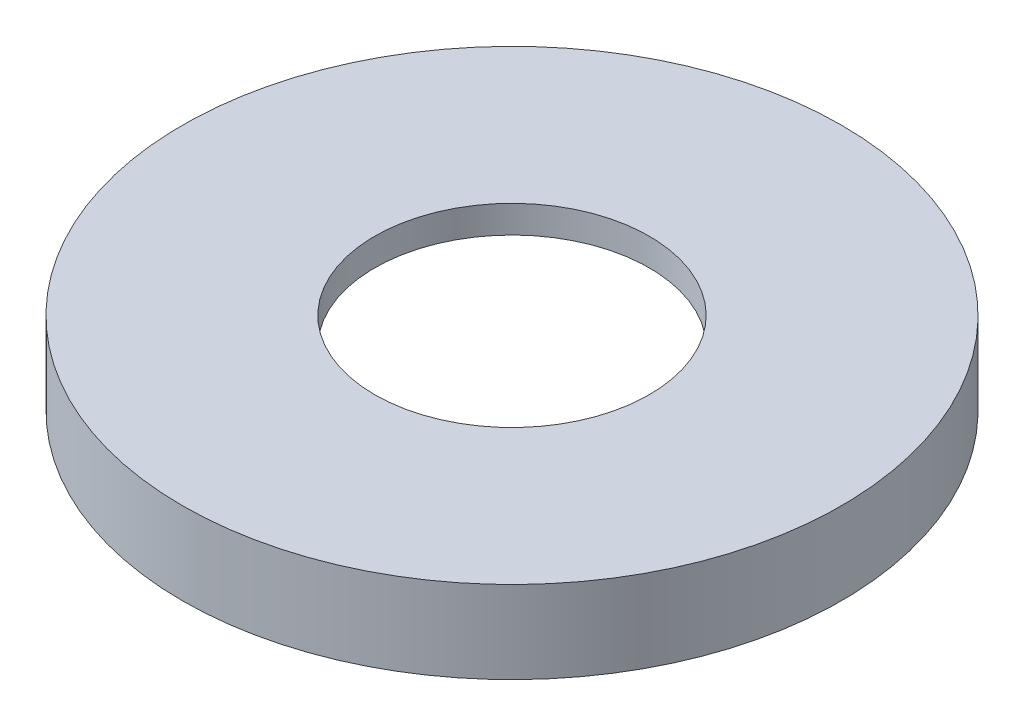
SolidWorks part; units mm, degrees
ref_plane "Front Plane" through (0, 0, 0) normal (0, 0, 1) x (1, 0, 0)
ref_plane "Top Plane" through (0, 0, 0) normal (0, 1, 0) x (1, 0, 0)
ref_plane "Right Plane" through (0, 0, 0) normal (1, 0, 0) x (0, 0, -1)
sketch "Sketch1" plane through (0, 0, 0) normal (0, 1, 0) x (1, 0, 0)
  circle A0 centre (0, 0) radius 33.0835
  circle A1 centre (0, 0) radius 38.1
  dimension "D1" = 66.167
  dimension "D2" = 76.2
extrude "Boss-Extrude1" add sketch "Sketch1" against normal blind 6.35
sketch "Sketch2" plane through (0, 0, 0) normal (0, 1, 0) x (1, 0, 0)
  circle A0 centre (0, 0) radius 38.1
  circle A19 centre (0, 0) radius 15.875
  dimension "D2" = 76.2
  dimension "D8" = 31.75
extrude "Boss-Extrude2" add sketch "Sketch2" along normal blind 3.175
